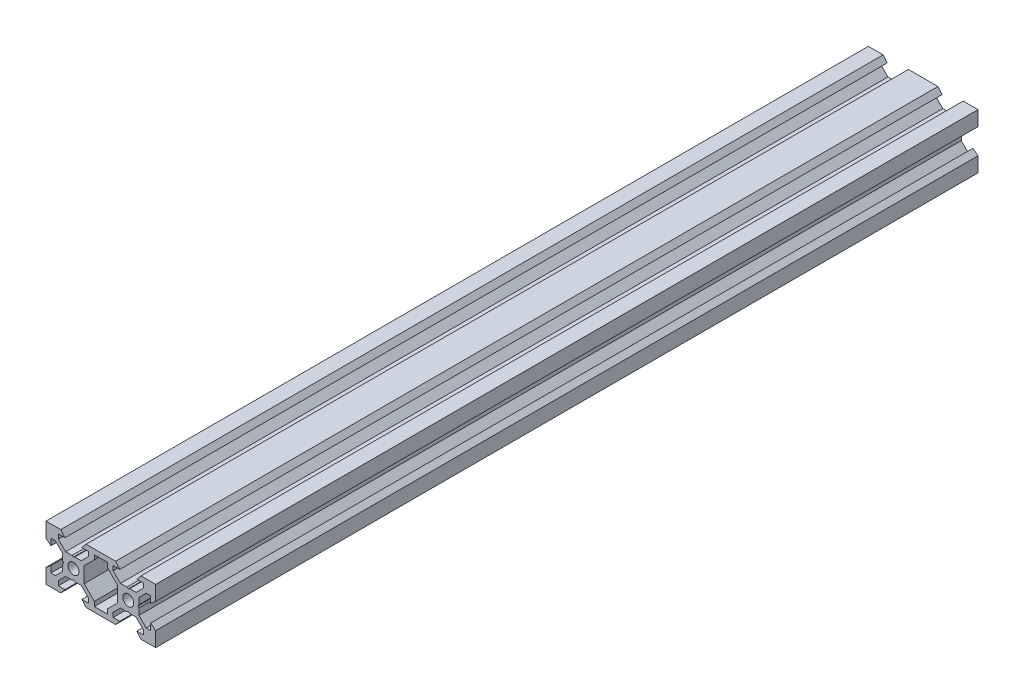
SolidWorks part; units mm, degrees
ref_plane "Front Plane" through (0, 0, 0) normal (0, 0, 1) x (1, 0, 0)
ref_plane "Top Plane" through (0, 0, 0) normal (0, 1, 0) x (1, 0, 0)
ref_plane "Right Plane" through (0, 0, 0) normal (1, 0, 0) x (0, 0, -1)
sketch "Sketch1" plane through (0, 0, 0) normal (0, 0, 1) x (1, 0, 0)
  line L0 (-5.3896, 10) -> (5.3896, 10)
  line L1 (0, 10) -> (0, 4.6104) construction
  line L2 (-6.1, -2.8393) -> (-2.3769, -6.5562)
  line L3 (5.3896, -10) -> (-5.3896, -10) construction
  line L5 (-6.1, 2.8393) -> (-6.1, -2.8393)
  line L6 (-4.5, 8.2) -> (-4.5, 6.5562)
  line L7 (2.3832, 6.5562) -> (2.3832, 8.2)
  line L9 (-6.1, 2.8393) -> (-2.3832, 6.5562)
  line L10 (-4.5, 6.5562) -> (-7.1607, 3.9)
  line L11 (-2.3832, 6.5562) -> (-2.3832, 8.2)
  line L12 (-5.3896, 10) -> (-6.9, 8.2)
  line L13 (6.1, 2.8393) -> (2.3832, 6.5562)
  line L14 (-6.9, 8.2) -> (-4.5, 8.2)
  line L15 (-16.5562, 5.5) -> (-18.2, 5.5)
  line L16 (0, 0) -> (6.1, 0) construction
  line L17 (-6.9, -8.2) -> (-4.5, -8.2)
  line L18 (-2.3769, -6.5562) -> (-2.3769, -8.2)
  line L19 (-5.3896, -10) -> (-6.9, -8.2)
  line L20 (2.3769, -6.5562) -> (2.3769, -8.2)
  line L21 (-9.4804, -3.9002) -> (-10, -3.6002)
  line L22 (-9.4804, 3.8998) -> (-10, 3.5998)
  line L23 (6.1, -2.8393) -> (2.3769, -6.5562)
  line L24 (-2.3769, -8.2) -> (2.3769, -8.2)
  line L25 (-2.3832, 8.2) -> (2.3832, 8.2)
  line L26 (-9.4804, 3.8998) -> (-7.1607, 3.9)
  line L27 (-5.3896, -10) -> (5.3896, -10)
  line L28 (-9.4804, -3.9002) -> (-7.1604, -3.9002)
  line L29 (-4.5, -6.5562) -> (-7.1607, -3.9)
  line L30 (-20, 10) -> (20, 10) construction
  line L32 (6.1, 2.8393) -> (6.1, -2.8393)
  line L33 (-4.5, -8.2) -> (-4.5, -6.5562)
  line L34 (-16.5562, -5.5) -> (-18.2, -5.5)
  line L36 (-10, 0) -> (-10, 8.2) construction
  line L37 (-20, -10) -> (-14.6104, -10) construction
  line L38 (-20, -10) -> (-20, -4.6104) construction
  line L39 (-20, 10) -> (-20, 4.6104) construction
  line L40 (-20, 10) -> (-14.6104, 10) construction
  line L41 (-20, -10) -> (-20, -4.6104)
  line L42 (-15.5, -8.2) -> (-15.5, -6.5562)
  line L43 (-20, -10) -> (-14.6104, -10)
  line L44 (7.1519, 3.8998) -> (9.4804, 3.8998)
  line L45 (-16.5562, -5.5) -> (-13.9, -2.8393)
  line L46 (-15.5, -6.5562) -> (-12.8393, -3.9)
  line L47 (-12.8393, -3.9) -> (-10.5196, -3.9002)
  line L48 (-13.9, -2.8393) -> (-13.9, -0.5196)
  line L49 (-12.8393, 3.9) -> (-10.5196, 3.8998)
  line L50 (-13.9, 0.5196) -> (-13.9, 2.8393)
  line L51 (-13.9, 0.5196) -> (-13.6, 0)
  line L52 (-13.6, 0) -> (-13.9, -0.5196)
  line L53 (-10.5196, 3.8998) -> (-10, 3.5998)
  line L54 (-10.5196, -3.9002) -> (-10, -3.6002)
  line L55 (-20, -4.6104) -> (-18.2, -3.1)
  line L56 (-14.6104, -10) -> (-13.1, -8.2)
  line L57 (-18.2, -3.1) -> (-18.2, -5.5)
  line L58 (-13.1, -8.2) -> (-15.5, -8.2)
  line L59 (-20, -10) -> (20, -10) construction
  line L60 (-20, -10) -> (-20, 10) construction
  line L61 (-13.1, 8.2) -> (-15.5, 8.2)
  line L62 (-18.2, 3.1) -> (-18.2, 5.5)
  line L63 (-14.6104, 10) -> (-13.1, 8.2)
  line L64 (-20, 4.6104) -> (-18.2, 3.1)
  line L65 (-15.5, 6.5562) -> (-12.8393, 3.9)
  line L66 (-16.5562, 5.5) -> (-13.9, 2.8393)
  line L67 (-20, 10) -> (-20, 4.6104)
  line L68 (-20, 10) -> (-14.6104, 10)
  line L69 (-15.5, 8.2) -> (-15.5, 6.5562)
  line L70 (4.5, 6.5562) -> (7.1519, 3.8998)
  line L71 (15.5, 6.5562) -> (12.8481, 3.8998)
  line L72 (0, -10) -> (0, 10) construction
  line L73 (-20, -10) -> (0, 10) construction
  line L74 (10.5196, 3.8998) -> (12.8481, 3.8998)
  line L75 (12.8393, -3.9) -> (10.5192, -3.9)
  line L76 (20, -10) -> (0, 10) construction
  line L77 (20, -10) -> (20, 10) construction
  line L78 (20, 10) -> (14.6104, 10) construction
  line L79 (20, 10) -> (20, 4.6104) construction
  line L80 (20, -10) -> (20, -4.6104) construction
  line L81 (20, -10) -> (14.6104, -10) construction
  line L82 (10, 0) -> (10, 8.2) construction
  line L83 (20, 10) -> (20, 4.6104)
  line L84 (15.5, 8.2) -> (15.5, 6.5562)
  line L85 (20, 10) -> (14.6104, 10)
  line L87 (16.5562, 5.5) -> (13.9, 2.8393)
  line L89 (20, 4.6104) -> (18.2, 3.1)
  line L90 (14.6104, 10) -> (13.1, 8.2)
  line L91 (18.2, 3.1) -> (18.2, 5.5)
  line L92 (13.1, 8.2) -> (15.5, 8.2)
  line L93 (13.1, -8.2) -> (15.5, -8.2)
  line L94 (18.2, -3.1) -> (18.2, -5.5)
  line L95 (14.6104, -10) -> (13.1, -8.2)
  line L96 (20, -4.6104) -> (18.2, -3.1)
  line L97 (10.5196, -3.9002) -> (10, -3.6002)
  line L98 (10.5196, 3.8998) -> (10, 3.5998)
  line L99 (13.6, 0) -> (13.9, -0.5196)
  line L100 (13.9, 0.5196) -> (13.6, 0)
  line L101 (13.9, 0.5196) -> (13.9, 2.8393)
  line L102 (9.4808, -3.9) -> (7.1607, -3.9)
  line L103 (13.9, -2.8393) -> (13.9, -0.5196)
  line L105 (15.5, -6.5562) -> (12.8393, -3.9)
  line L106 (16.5562, -5.5) -> (13.9, -2.8393)
  line L107 (20, -10) -> (20, -4.6104)
  line L108 (20, -10) -> (14.6104, -10)
  line L109 (15.5, -8.2) -> (15.5, -6.5562)
  line L111 (16.5562, -5.5) -> (18.2, -5.5)
  line L112 (4.5, -8.2) -> (4.5, -6.5562)
  line L114 (4.5, -6.5562) -> (7.1607, -3.9)
  line L121 (9.4804, 3.8998) -> (10, 3.5998)
  line L122 (9.4804, -3.9002) -> (10, -3.6002)
  line L124 (5.3896, -10) -> (6.9, -8.2)
  line L126 (6.9, -8.2) -> (4.5, -8.2)
  line L128 (16.5562, 5.5) -> (18.2, 5.5)
  line L129 (6.9, 8.2) -> (4.5, 8.2)
  line L131 (5.3896, 10) -> (6.9, 8.2)
  line L135 (4.5, 8.2) -> (4.5, 6.5562)
  circle A0 centre (-10, 0) radius 2
  circle A1 centre (10, 0) radius 2
  dimension "D14" = 4
  dimension "D1" = 20
  dimension "D2" = 5.3896
  dimension "D3" = 1.8
  dimension "D4" = 1.5104
  dimension "D5" = 4.5
  dimension "D6" = 5.5
  dimension "D7" = 120
  dimension "D8" = 0.3
  dimension "D9" = 2.3197
  dimension "D10" = 7.8
  dimension "D11" = 20
  dimension "D12" = 1.5
  dimension "D13" = 2.6607
  dimension "D15" = 50
  dimension "D16" = 1.5
  dimension "D17" = 1.8
  dimension "D18" = 16.4
  dimension "D19" = 2.3832
  dimension "D20" = 45
extrude "Boss-Extrude1" add sketch "Sketch1" along normal blind 300
